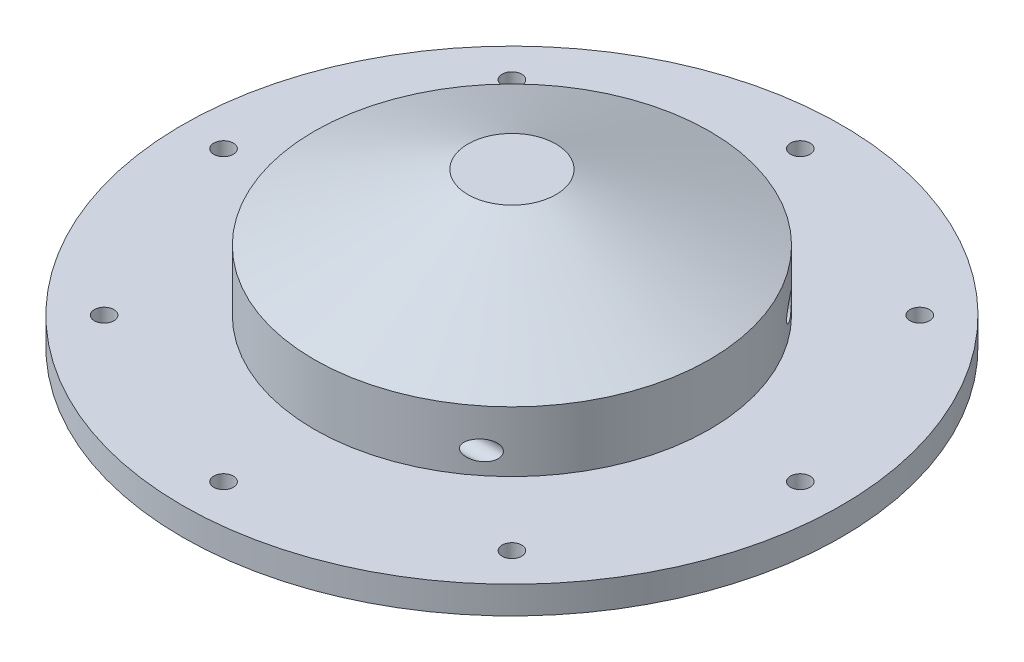
SolidWorks part; units mm, degrees
ref_plane "Front Plane" through (0, 0, 0) normal (0, 0, 1) x (1, 0, 0)
ref_plane "Top Plane" through (0, 0, 0) normal (0, 1, 0) x (1, 0, 0)
ref_plane "Right Plane" through (0, 0, 0) normal (1, 0, 0) x (0, 0, -1)
sketch "Sketch2" plane through (0, 0, 0) normal (0, 1, 0) x (1, 0, 0)
  circle A0 centre (0, 0) radius 38.1
  dimension "D1" = 76.2
extrude "Boss-Extrude1" add sketch "Sketch2" along normal blind 3.175
hole_wizard "Tap Drill for #4-40 Tap1" positions "Sketch3" profile "Sketch4" hole size "#4-40" standard "ANSI Inch" end condition through all
sketch "Sketch3" plane through (0, 0, 0) normal (0, -1, 0) x (-1, 0, 0)
  point P0 (0, -33.3375)
  dimension "D1" = 33.3375
sketch "Sketch4" plane through (0, 0, 33.3375) normal (1, 0, 0) x (0, 0, -1)
  line L0 (0, 0) -> (0, 3.175)
  line L1 (0, 3.175) -> (1.1303, 3.175)
  line L2 (1.1303, 3.175) -> (1.1303, 0)
  line L5 (1.1303, 0) -> (0, 0)
  line L11 (0, -6.35) -> (0, 107.95) construction
  dimension "Thru Hole Dia." = 2.2606
  dimension "Thru Hole Depth" = 3.175
pattern_circular "CirPattern1" count 8 over 360 about axis through (0, 0, 0) along (0, 1, 0) of "Tap Drill for #4-40 Tap1"
sketch "Sketch5" plane through (0, 3.175, 0) normal (0, 1, 0) x (1, 0, 0)
  circle A0 centre (0, 0) radius 28.575
  dimension "D1" = 57.15
sketch "Sketch7" plane through (0, 3.175, 0) normal (0, 1, 0) x (1, 0, 0)
  circle A0 centre (0, 0) radius 22.86
  dimension "D1" = 45.72
extrude "Boss-Extrude2" add sketch "Sketch7" along normal blind 6.985
sketch "Sketch8" plane through (0, 0, 0) normal (0, -1, 0) x (1, 0, 0)
  circle A0 centre (0, 0) radius 19.05
  dimension "D1" = 38.1
extrude "Cut-Extrude1" cut sketch "Sketch8" against normal blind 8.255
hole_wizard "Tap Drill for #4-40 Tap2" positions "Sketch11" profile "Sketch12" hole size "#4-40" standard "ANSI Inch"
sketch "Sketch11" plane through (0, 0, 0) normal (0, 0, 1) x (1, 0, 0)
  line L0 (0, -1.7463) -> (0, 1.7463) construction
  line L1 (22.86, 3.175) -> (-22.86, 3.175) construction
  point P0 (-17.78, 5.715)
  point P10 (0, 0)
  dimension "D1" = 17.78
  dimension "D2" = 2.54
sketch "Sketch12" plane through (-17.78, 5.715, 0) normal (1, 0, 0) x (0, 1, 0)
  line L0 (0, 0) -> (0, 38.1)
  line L1 (0, 38.1) -> (1.1303, 38.1)
  line L2 (1.1303, 38.1) -> (1.1303, 0)
  line L5 (1.1303, 0) -> (0, 0)
  line L11 (0, -6.35) -> (0, 107.95) construction
  dimension "Thru Hole Dia." = 2.2606
  dimension "Thru Hole Depth" = 38.1
pattern_circular "CirPattern2" count 4 over 360 about axis through (0, 10.16, 0) along (0, 1, 0) of "Tap Drill for #4-40 Tap2"
sketch "Sketch13" plane through (0, 10.16, 0) normal (0, 1, 0) x (1, 0, 0)
  circle A0 centre (0, 0) radius 22.86
  circle A1 centre (0, 0) radius 22.86 construction
  dimension "D1" = 0
ref_plane "Plane2" through (0, 17.78, 0) normal (0, 1, 0) x (1, 0, 0)
sketch "Sketch14" plane through (0, 17.78, 0) normal (0, 1, 0) x (1, 0, 0)
  circle A0 centre (0, 0) radius 5.08
  dimension "D1" = 10.16
loft "Loft2" add profiles "Sketch14", "Sketch13"
